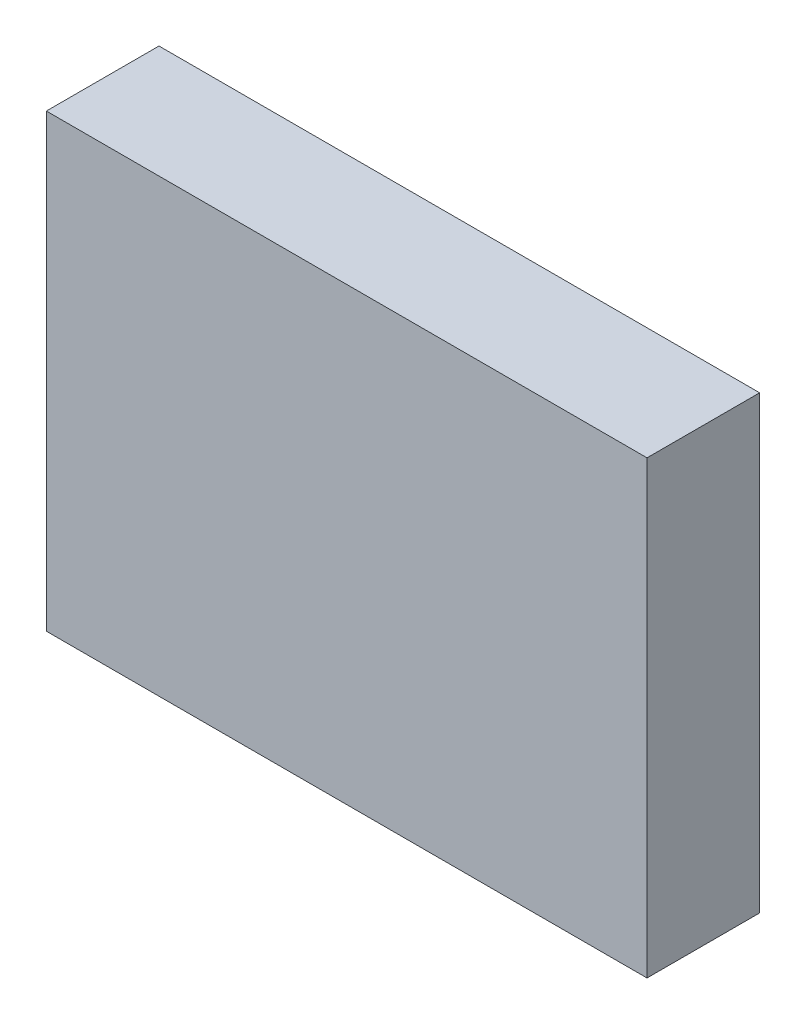
SolidWorks part; units mm, degrees
ref_plane "Front Plane" through (0, 0, 0) normal (0, 0, 1) x (1, 0, 0)
ref_plane "Top Plane" through (0, 0, 0) normal (0, 1, 0) x (1, 0, 0)
ref_plane "Right Plane" through (0, 0, 0) normal (1, 0, 0) x (0, 0, -1)
sketch "Sketch1" plane through (0, 0, 0) normal (0, 0, 1) x (1, 0, 0)
  line L1 (16, 12) -> (-16, 12)
  line L2 (16, 12) -> (16, -12)
  line L3 (16, -12) -> (-16, -12)
  line L4 (-16, 12) -> (-16, -12)
  line L5 (16, 12) -> (-16, -12) construction
  line L6 (16, -12) -> (-16, 12) construction
  point P0 (0, 0)
  point P5 (-131.7062, -15.266)
  point P6 (0, 0)
  dimension "D1" = 32
  dimension "D2" = 24
extrude "Boss-Extrude1" add sketch "Sketch1" along normal blind 6
